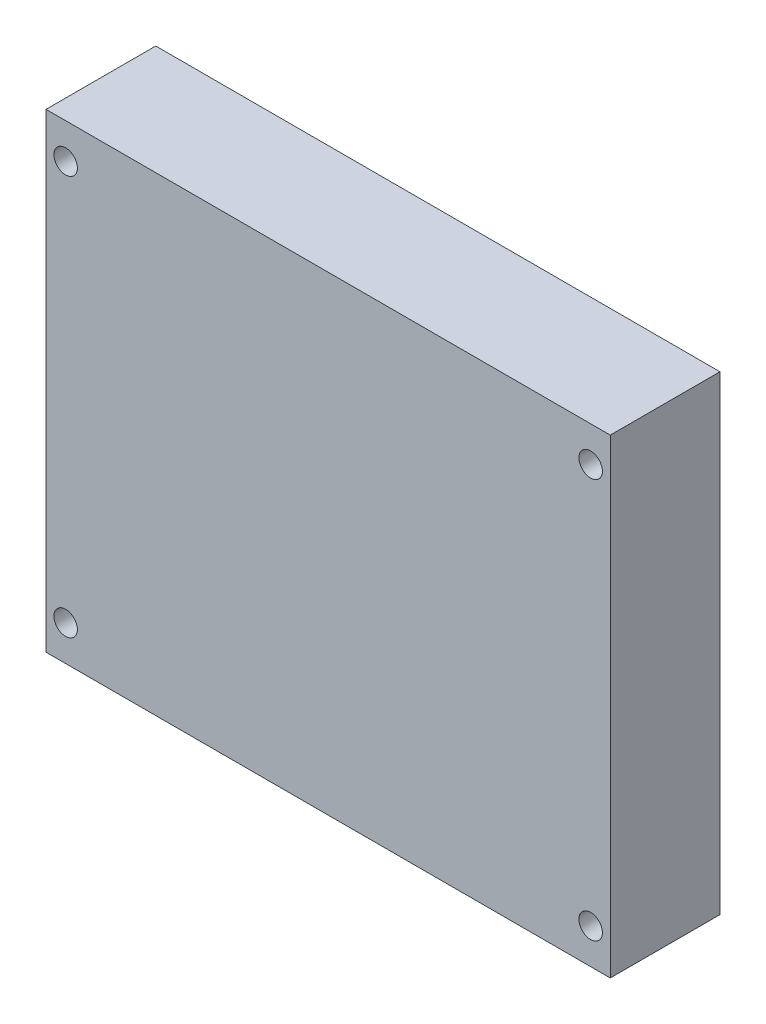
SolidWorks part; units mm, degrees
ref_plane "Alzado" through (0, 0, 0) normal (0, 0, 1) x (1, 0, 0)
ref_plane "Planta" through (0, 0, 0) normal (0, 1, 0) x (1, 0, 0)
ref_plane "Vista lateral" through (0, 0, 0) normal (1, 0, 0) x (0, 0, -1)
sketch "Croquis1" plane through (0, 0, 0) normal (0, 0, 1) x (1, 0, 0)
  line L0 (2.5, 55.5) -> (2.5, 4.5) construction
  line L1 (0, 0) -> (72, 0)
  line L2 (0, 0) -> (0, 60)
  line L3 (0, 60) -> (72, 60)
  line L4 (72, 0) -> (72, 60)
  line L5 (2.5, 4.5) -> (69.5, 4.5) construction
  line L6 (69.5, 4.5) -> (69.5, 55.5) construction
  line L7 (69.5, 55.5) -> (2.5, 55.5) construction
  circle A0 centre (2.5, 55.5) radius 1.5
  circle A1 centre (69.5, 55.5) radius 1.5
  circle A2 centre (69.5, 4.5) radius 1.5
  circle A3 centre (2.5, 4.5) radius 1.5
  dimension "D3" = 3
  dimension "D1" = 72
  dimension "D2" = 60
  dimension "D4" = 67
  dimension "D5" = 51
  dimension "D6" = 2.5
  dimension "D7" = 4.5
extrude "Saliente-Extruir1" add sketch "Croquis1" along normal blind 14
